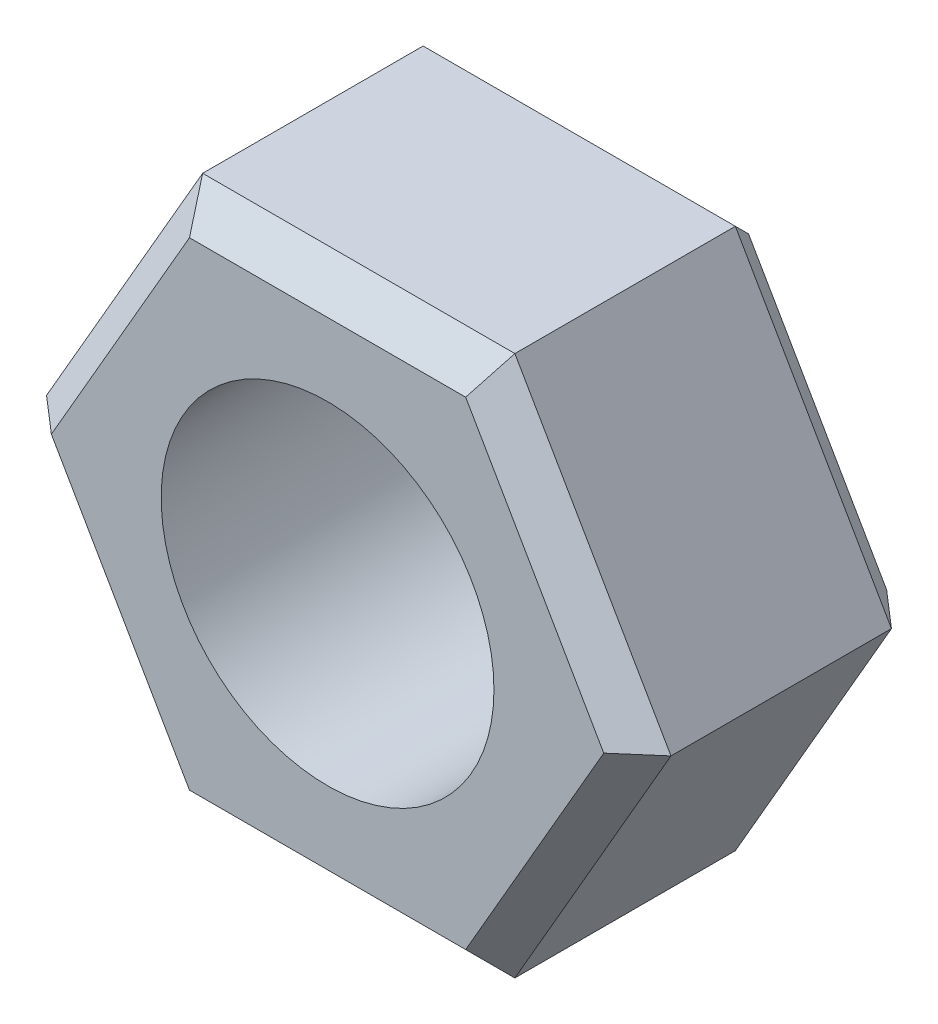
SolidWorks part; units mm, degrees
ref_plane "Спереди" through (0, 0, 0) normal (0, 0, 1) x (1, 0, 0)
ref_plane "Сверху" through (0, 0, 0) normal (0, 1, 0) x (1, 0, 0)
ref_plane "Справа" through (0, 0, 0) normal (1, 0, 0) x (0, 0, -1)
sketch "Эскиз1" plane through (0, 0, 0) normal (0, 0, 1) x (1, 0, 0)
  line L1 (3.7528, -6.5) -> (7.5056, 0)
  line L2 (7.5056, 0) -> (3.7528, 6.5)
  line L3 (3.7528, 6.5) -> (-3.7528, 6.5)
  line L4 (-3.7528, 6.5) -> (-7.5056, 0)
  line L5 (-7.5056, 0) -> (-3.7528, -6.5)
  line L6 (-3.7528, -6.5) -> (3.7528, -6.5)
  circle A0 centre (0, 0) radius 6.5 construction
  circle A1 centre (0, 0) radius 4
extrude "Бобышка-Вытянуть1" add sketch "Эскиз1" along normal blind 6.8
chamfer "Фаска1" distance 0.75 angle 45 12 edges at (-5.6292, -3.25, 6.8) (-5.6292, 3.25, 6.8) (0, 6.5, 6.8) (5.6292, 3.25, 6.8) (5.6292, -3.25, 6.8) (0, -6.5, 6.8) (0, -6.5, 0) (5.6292, -3.25, 0) (5.6292, 3.25, 0) (0, 6.5, 0) (-5.6292, 3.25, 0) (-5.6292, -3.25, 0)
